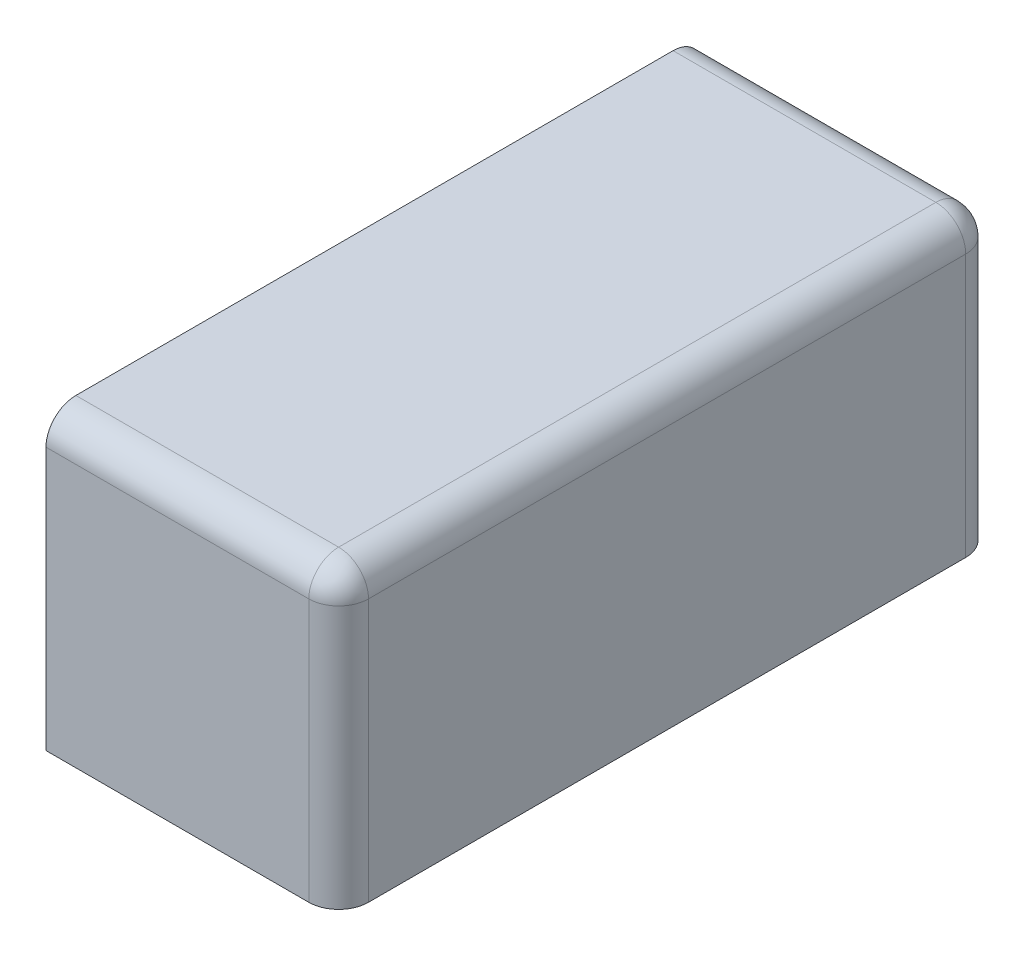
SolidWorks part; units mm, degrees
ref_plane "Alzado" through (0, 0, 0) normal (0, 0, 1) x (1, 0, 0)
ref_plane "Planta" through (0, 0, 0) normal (0, 1, 0) x (1, 0, 0)
ref_plane "Vista lateral" through (0, 0, 0) normal (1, 0, 0) x (0, 0, -1)
sketch "Croquis1" plane through (0, 0, 0) normal (0, 0, 1) x (1, 0, 0)
  line L1 (0, 0) -> (-9.8, 0)
  line L2 (0, 0) -> (0, 9.8)
  line L3 (0, 9.8) -> (-9.8, 9.8)
  line L4 (-9.8, 0) -> (-9.8, 9.8)
  dimension "D1" = 9.8
  dimension "D2" = 9.8
extrude "Saliente-Extruir1" add sketch "Croquis1" along normal blind 22
fillet "Redondeo1" radius 1 5 edges at (-4.9, 9.8, 0) (0, 4.9, 0) (-4.9, 9.8, 22) (0, 4.9, 22) (0, 9.8, 11)
sketch "Croquis2" plane through (-9.8, 0, 0) normal (-1, 0, 0) x (0, 0, 1)
  line L0 (0, 4.4) -> (22, 4.4) construction
  line L1 (0, 8.8) -> (0, 0) construction
  line L2 (22, 8.8) -> (22, 0) construction
  line L3 (11, 9.8) -> (11, 0) construction
  line L4 (21, 9.8) -> (1, 9.8) construction
  line L5 (22, 0) -> (0, 0) construction
  circle A0 centre (11, 4.4) radius 1.5
  dimension "D1" = 3
extrude "Cortar-Extruir1" cut sketch "Croquis2" against normal blind 7
sketch "Croquis3" plane through (0, 0, 0) normal (0, -1, 0) x (1, 0, 0)
  line L0 (-5.4, 22) -> (-5.4, 0) construction
  line L1 (-9.8, 22) -> (-1, 22) construction
  line L2 (-9.8, 0) -> (-1, 0) construction
  circle A0 centre (-5.4, 18.5) radius 2
  circle A1 centre (-5.4, 3.5) radius 2
  dimension "D3" = 4
  dimension "D4" = 4
  dimension "D1" = 3.5
  dimension "D2" = 3.5
extrude "Cortar-Extruir2" cut sketch "Croquis3" against normal blind 5.2
